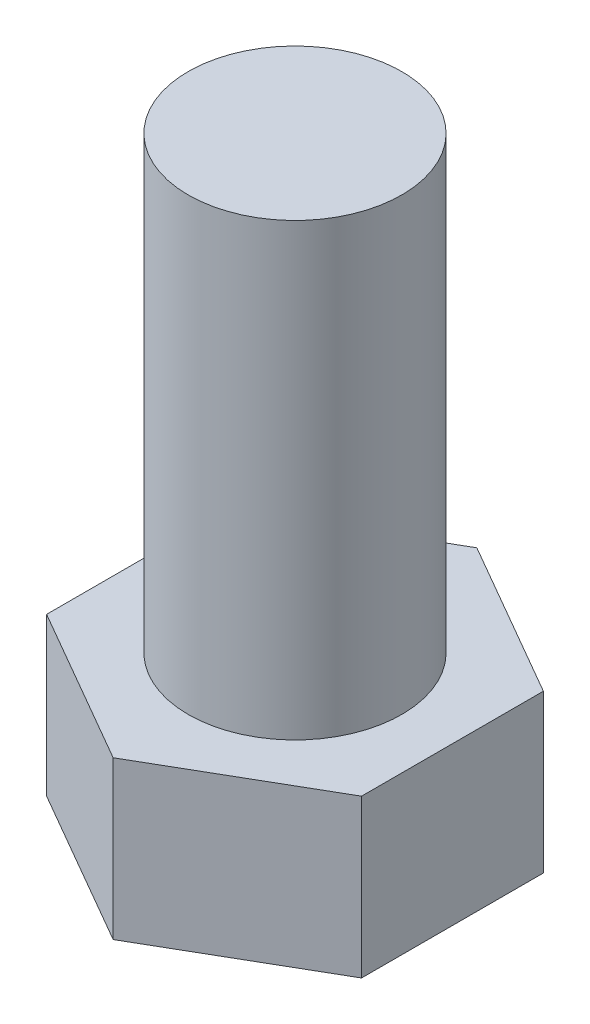
SolidWorks part; units mm, degrees
ref_plane "Front Plane" through (0, 0, 0) normal (0, 0, 1) x (1, 0, 0)
ref_plane "Top Plane" through (0, 0, 0) normal (0, 1, 0) x (1, 0, 0)
ref_plane "Right Plane" through (0, 0, 0) normal (1, 0, 0) x (0, 0, -1)
sketch "Sketch1" plane through (0, 0, 0) normal (0, 1, 0) x (1, 0, 0)
  line L1 (0, 8.0829) -> (-7, 4.0415)
  line L2 (-7, 4.0415) -> (-7, -4.0415)
  line L3 (-7, -4.0415) -> (0, -8.0829)
  line L4 (0, -8.0829) -> (7, -4.0415)
  line L5 (7, -4.0415) -> (7, 4.0415)
  line L6 (7, 4.0415) -> (0, 8.0829)
  circle A0 centre (0, 0) radius 7 construction
  dimension "D1" = 14
extrude "Boss-Extrude1" add sketch "Sketch1" along normal blind 7
sketch "Sketch2" plane through (0, 7, 0) normal (0, 1, 0) x (1, 0, 0)
  circle A0 centre (0, 0) radius 4.75
  dimension "D1" = 9.5
extrude "Boss-Extrude2" add sketch "Sketch2" along normal blind 20
cosmetic thread "Cosmetic Thread1" parameters "D2"=6.891
cosmetic thread "Cosmetic Thread2" parameters "D2"=6.891
